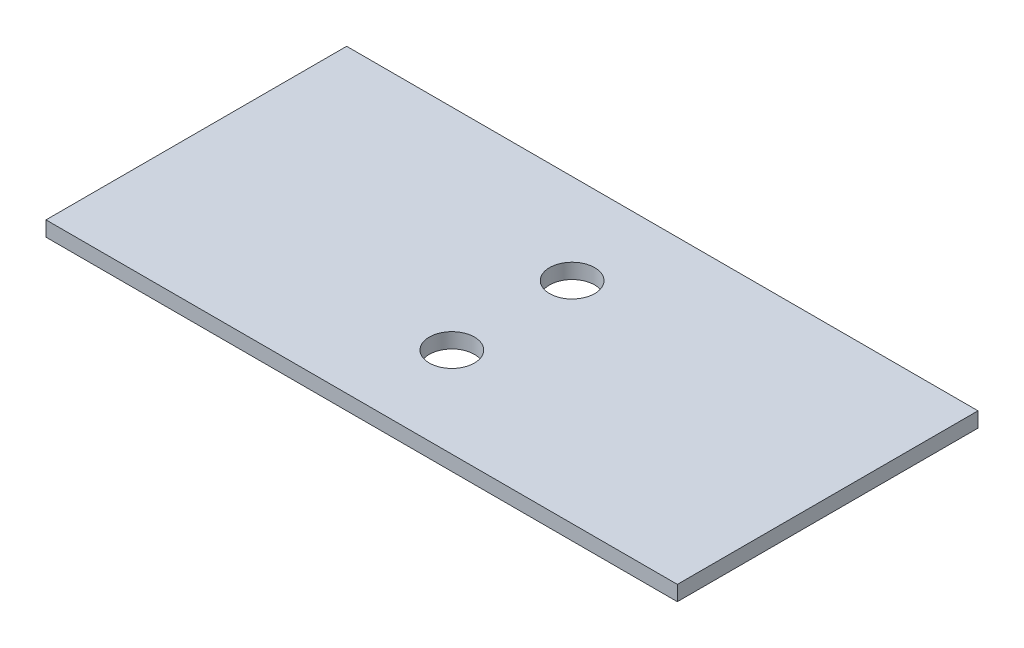
SolidWorks part; units mm, degrees
material "Простая углеродистая сталь"
ref_plane "Спереди" through (0, 0, 0) normal (0, 0, 1) x (1, 0, 0)
ref_plane "Сверху" through (0, 0, 0) normal (0, 1, 0) x (1, 0, 0)
ref_plane "Справа" through (0, 0, 0) normal (1, 0, 0) x (0, 0, -1)
sketch "Эскиз1" plane through (0, 0, 0) normal (0, 1, 0) x (1, 0, 0)
  line L0 (42, 10) -> (0, 10) construction
  line L1 (0, 0) -> (42, 0)
  line L2 (0, 0) -> (0, 20)
  line L3 (0, 20) -> (42, 20)
  line L4 (42, 0) -> (42, 20)
  circle A0 centre (21, 14) radius 1.5
  circle A1 centre (21, 6) radius 1.5
  dimension "D1" = 42
  dimension "D2" = 20
extrude "Бобышка-Вытянуть1" add sketch "Эскиз1" along normal blind 1
